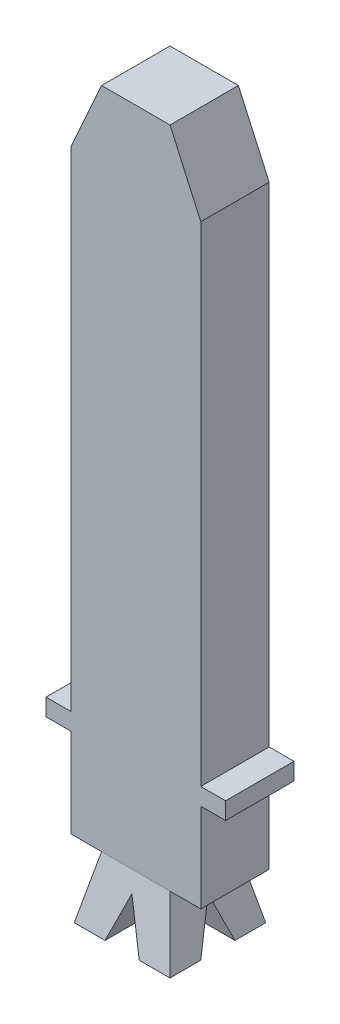
SolidWorks part; units mm, degrees
ref_plane "Front Plane" through (0, 0, 0) normal (0, 0, 1) x (1, 0, 0)
ref_plane "Top Plane" through (0, 0, 0) normal (0, 1, 0) x (1, 0, 0)
ref_plane "Right Plane" through (0, 0, 0) normal (1, 0, 0) x (0, 0, -1)
sketch "Sketch1" plane through (0, 0, 0) normal (0, 0, 1) x (1, 0, 0)
  line L0 (1.9, 0) -> (2.625, 0)
  line L2 (-1.9, 14.3) -> (-1.9, 0)
  line L4 (1.9, 14.3) -> (1.9, 0)
  line L5 (-2.625, 0) -> (-1.9, 0)
  line L6 (-2.625, 0) -> (-2.625, -0.5)
  line L7 (-2.625, -0.5) -> (-1.9, -0.5)
  line L8 (2.625, 0) -> (2.625, -0.5)
  line L9 (1.9, -0.5) -> (2.625, -0.5)
  line L11 (-1.9, -0.5) -> (-1.9, -3.1)
  line L12 (-1.9, -3.1) -> (1.9, -3.1)
  line L13 (1.9, -0.5) -> (1.9, -3.1)
  line L14 (-1, 16.3) -> (1, 16.3)
  line L15 (-1.9, 14.3) -> (-1, 16.3)
  line L16 (1, 16.3) -> (1.9, 14.3)
  point P9 (2.625, -0.25)
  dimension "D2" = 3.8
  dimension "D3" = 1.9
  dimension "D5" = 5.25
  dimension "D6" = 2.625
  dimension "D1" = 2.6
  dimension "D7" = 1.9
  dimension "D8" = 1.9
  dimension "D9" = 0.25
  dimension "D10" = 0.5
  dimension "D11" = 2
  dimension "D13" = 0.9
  dimension "D14" = 3.8
  dimension "D4" = 14.3
  dimension "D12" = 16.3
extrude "Boss-Extrude1" add sketch "Sketch1" along normal blind 2
ref_plane "Plane1" through (0, -4.9, 0) normal (0, -1, 0) x (-1, 0, 0)
sketch "Sketch2" plane through (0, -3.1, 0) normal (0, -1, 0) x (1, 0, 0)
  line L0 (-1.9, 2) -> (1.9, 2) construction
  line L1 (-1, 2) -> (1, 2)
  line L2 (-1, 2) -> (-1, 0)
  line L3 (-1, 0) -> (1, 0)
  line L4 (1, 2) -> (1, 0)
  line L5 (-1.9, 0) -> (1.9, 0) construction
  dimension "D1" = 2
  dimension "D2" = 2
  dimension "D3" = 1
sketch "Sketch3" plane through (0, -4.9, 0) normal (0, -1, 0) x (-1, 0, 0)
  line L1 (-1.4, 0.4) -> (1.4, 0.4)
  line L2 (-1.4, 0.4) -> (-1.4, -2.4)
  line L3 (-1.4, -2.4) -> (1.4, -2.4)
  line L4 (1.4, 0.4) -> (1.4, -2.4)
  dimension "D1" = 2.8
  dimension "D2" = 2.8
  dimension "D3" = 1.4
  dimension "D4" = 0.4
loft "Loft1" add profiles "Sketch2", "Sketch3"
ref_plane "Plane2" through (0, 0, 1.8) normal (0, 0, 1) x (1, 0, 0)
sketch "Sketch4" plane through (0, 0, 1.8) normal (0, 0, 1) x (1, 0, 0)
  line L0 (0, -3.6115) -> (-0.5, -4.9)
  line L1 (-1.1, -4.9) -> (1.1, -4.9) construction
  line L2 (-0.5, -4.9) -> (0.5, -4.9)
  line L3 (0.5, -4.9) -> (0, -3.6115)
  dimension "D1" = 0.5
  dimension "D2" = 0.5
  dimension "D3" = 3.6115
ref_plane "Plane3" through (1.8, 0, 0) normal (1, 0, 0) x (0, 0, -1)
sketch "Sketch5" plane through (1.8, 0, -1.8) normal (-1, 0, 0) x (0, 0, 1)
  line L0 (2.8, -3.6115) -> (2.3, -4.9)
  line L1 (1.4, -4.9) -> (4.2, -4.9) construction
  line L2 (2.3, -4.9) -> (3.3, -4.9)
  line L3 (3.3, -4.9) -> (2.8, -3.6115)
  line L4 (1.4, -4.9) -> (4.2, -4.9) construction
extrude "Cut-Extrude1" cut sketch "Sketch4" against normal through all both and the other way through all
extrude "Cut-Extrude2" cut sketch "Sketch5" against normal through all both and the other way through all
equation "\"D3@Sketch1\"=\"D2@Sketch1\"/2"
equation "\"D6@Sketch1\"=\"D5@Sketch1\"/2"
equation "\"D3@Sketch3\"=\"D1@Sketch3\"/2"
equation "\"D4@Sketch3\"=(\"D2@Sketch3\"-2)/2"
